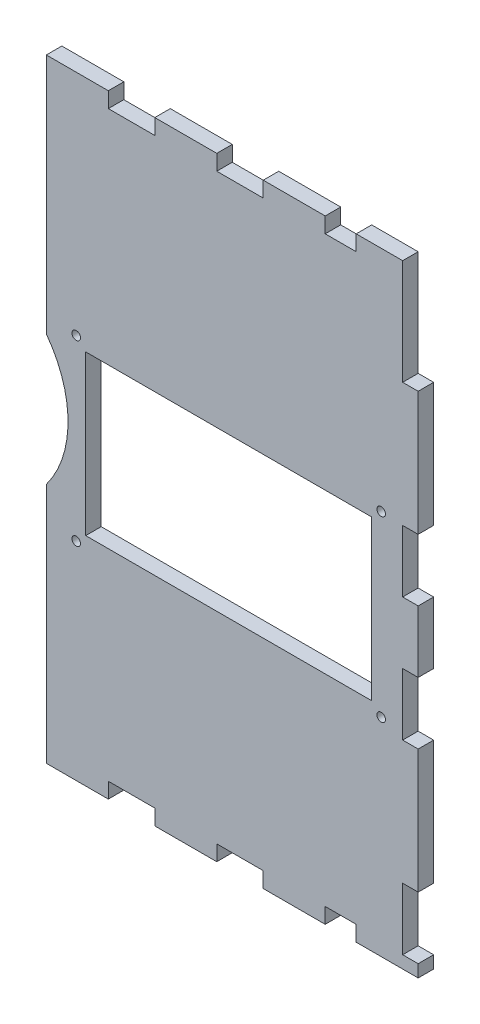
SolidWorks part; units mm, degrees
ref_plane "Front Plane" through (0, 0, 0) normal (0, 0, 1) x (1, 0, 0)
ref_plane "Top Plane" through (0, 0, 0) normal (0, 1, 0) x (1, 0, 0)
ref_plane "Right Plane" through (0, 0, 0) normal (1, 0, 0) x (0, 0, -1)
sketch "Sketch1" plane through (0, 0, 0) normal (0, 0, 1) x (1, 0, 0)
  line L1 (-133.35, 5.08) -> (-285.75, 5.08)
  line L2 (-133.35, 5.08) -> (-133.35, -246.38)
  line L3 (-133.35, -246.38) -> (-285.75, -246.38)
  line L4 (-285.75, 5.08) -> (-285.75, -246.38)
extrude "Boss-Extrude1" add sketch "Sketch1" along normal blind 6.35
sketch "Sketch2" plane through (0, 5.08, 0) normal (0, 1, 0) x (1, 0, 0)
  line L0 (-133.35, -6.35) -> (-285.75, -6.35) construction
  line L1 (-260.35, -6.35) -> (-241.3, -6.35)
  line L2 (-260.35, -6.35) -> (-260.35, 0)
  line L3 (-260.35, 0) -> (-241.3, 0)
  line L4 (-241.3, -6.35) -> (-241.3, 0)
  line L5 (-133.35, 0) -> (-285.75, 0) construction
  line L6 (-285.75, -6.35) -> (-285.75, 0) construction
  line L7 (-215.9, -6.35) -> (-196.85, -6.35)
  line L8 (-215.9, -6.35) -> (-215.9, 0)
  line L9 (-215.9, 0) -> (-196.85, 0)
  line L10 (-196.85, -6.35) -> (-196.85, 0)
  line L11 (-171.45, -6.35) -> (-158.75, -6.35)
  line L12 (-171.45, -6.35) -> (-171.45, 0)
  line L13 (-171.45, 0) -> (-158.75, 0)
  line L14 (-158.75, -6.35) -> (-158.75, 0)
  line M9 (-133.35, 0) -> (-285.75, 0)
  line M11 (-285.75, -6.35) -> (-133.35, -6.35)
  dimension "D1" = 25.4
  dimension "D2" = 19.05
  dimension "D3" = 25.4
  dimension "D4" = 19.05
  dimension "D5" = 25.4
  dimension "D6" = 12.7
extrude "Cut-Extrude1" cut sketch "Sketch2" against normal blind 6.35 contours L4 L2 M11 M9 | L10 L8 M11 M9 | L14 L12 M11 M9
sketch "Sketch3" plane through (0, -246.38, 0) normal (0, -1, 0) x (1, 0, 0)
  line L0 (-285.75, 0) -> (-133.35, 0) construction
  line L1 (-260.35, 0) -> (-241.3, 0)
  line L2 (-260.35, 0) -> (-260.35, 6.35)
  line L3 (-260.35, 6.35) -> (-241.3, 6.35)
  line L4 (-241.3, 0) -> (-241.3, 6.35)
  line L5 (-285.75, 6.35) -> (-133.35, 6.35) construction
  line L6 (-285.75, 6.35) -> (-285.75, 0) construction
  line L7 (-215.9, 0) -> (-196.85, 0)
  line L8 (-215.9, 0) -> (-215.9, 6.35)
  line L9 (-215.9, 6.35) -> (-196.85, 6.35)
  line L10 (-196.85, 0) -> (-196.85, 6.35)
  line L11 (-171.45, 0) -> (-158.75, 0)
  line L12 (-171.45, 0) -> (-171.45, 6.35)
  line L13 (-171.45, 6.35) -> (-158.75, 6.35)
  line L14 (-158.75, 0) -> (-158.75, 6.35)
  line L16 (-196.85, 6.35) -> (-196.85, 0) construction
  dimension "D1" = 25.4
  dimension "D2" = 19.05
  dimension "D3" = 25.4
  dimension "D4" = 19.05
  dimension "D5" = 25.4
  dimension "D6" = 12.7
extrude "Cut-Extrude2" cut sketch "Sketch3" against normal blind 6.35 and the other way through all
sketch "Sketch4" plane through (0, 0, 6.35) normal (0, 0, 1) x (1, 0, 0)
  line L0 (-133.35, -246.38) -> (-133.35, 5.08) construction
  line L3 (-133.35, -215.9) -> (-139.7, -215.9)
  line L5 (-133.35, -165.1) -> (-139.7, -165.1)
  line L6 (-133.35, -165.1) -> (-133.35, -139.7)
  line L7 (-133.35, -139.7) -> (-139.7, -139.7)
  line L8 (-139.7, -165.1) -> (-139.7, -139.7)
  line L9 (-133.35, 5.08) -> (-158.75, 5.08) construction
  line L10 (-133.35, -114.3) -> (-139.7, -114.3)
  line L11 (-133.35, -114.3) -> (-133.35, -88.9)
  line L12 (-133.35, -88.9) -> (-139.7, -88.9)
  line L13 (-139.7, -114.3) -> (-139.7, -88.9)
  line L14 (-133.35, -38.1) -> (-139.7, -38.1)
  line L15 (-133.35, -38.1) -> (-133.35, 5.08)
  line L16 (-133.35, 5.08) -> (-139.7, 5.08)
  line L17 (-139.7, -38.1) -> (-139.7, 5.08)
  line L18 (-139.7, -215.9) -> (-139.7, -241.3)
  line L19 (-139.7, -241.3) -> (-133.35, -241.3)
  line L20 (-133.35, -241.3) -> (-133.35, -215.9)
  line L21 (-158.75, -246.38) -> (-133.35, -246.38) construction
  line M24 (-133.35, -246.38) -> (-133.35, 5.08)
  line M25 (-133.35, 5.08) -> (-158.75, 5.08)
  dimension "D2" = 6.35
  dimension "D3" = 6.35
  dimension "D4" = 6.35
  dimension "D5" = 25.4
  dimension "D6" = 50.8
  dimension "D7" = 25.4
  dimension "D8" = 25.4
  dimension "D9" = 25.4
  dimension "D10" = 50.8
  dimension "D11" = 43.18
  dimension "D12" = 5.08
extrude "Cut-Extrude3" cut sketch "Sketch4" against normal blind 6.35 contours L8 L5 L7 M24 | L13 L10 L12 M24 | L17 L14 M24 M25 | L18 L19 L3 M24
sketch "Sketch5" plane through (0, 0, 6.35) normal (0, 0, 1) x (1, 0, 0)
  line L0 (-285.75, 5.08) -> (-285.75, -246.38) construction
  circle A0 centre (-321.31, -120.65) radius 44.45
  dimension "D1" = 88.9
  dimension "D2" = 35.56
extrude "Cut-Extrude4" cut sketch "Sketch5" against normal through all
sketch "Sketch6" plane through (0, 0, 6.35) normal (0, 0, 1) x (1, 0, 0)
  line L0 (-133.35, -139.7) -> (-133.35, -114.3) construction
  line L1 (-278.51, -166.37) -> (-143.51, -166.37) construction
  line L2 (-278.51, -166.37) -> (-278.51, -83.37) construction
  line L3 (-278.51, -83.37) -> (-143.51, -83.37) construction
  line L4 (-143.51, -166.37) -> (-143.51, -83.37) construction
  line L5 (-278.51, -166.37) -> (-143.51, -83.37) construction
  line L6 (-278.51, -83.37) -> (-143.51, -166.37) construction
  line L7 (-241.3, -246.38) -> (-215.9, -246.38) construction
  line L8 (-269.62, -157.48) -> (-269.62, -92.26)
  line L9 (-269.62, -92.26) -> (-152.4, -92.26)
  line L10 (-152.4, -157.48) -> (-152.4, -92.26)
  line L11 (-269.62, -157.48) -> (-152.4, -157.48)
  circle A0 centre (-273.51, -161.37) radius 1.75
  circle A1 centre (-273.51, -88.37) radius 1.75
  circle A2 centre (-148.51, -88.37) radius 1.75
  circle A3 centre (-148.51, -161.37) radius 1.75
  point P0 (-211.01, -124.87)
  dimension "D6" = 3.5
  dimension "D7" = 3.5
  dimension "D8" = 3.5
  dimension "D9" = 3.5
  dimension "D10" = 5
  dimension "D11" = 5
  dimension "D12" = 5
  dimension "D13" = 5
  dimension "D14" = 5
  dimension "D15" = 5
  dimension "D16" = 5
  dimension "D17" = 5
  dimension "D1" = 135
  dimension "D2" = 83
  dimension "D3" = 10.16
  dimension "D4" = 80.01
  dimension "D5" = 8.89
extrude "Cut-Extrude5" cut sketch "Sketch6" against normal through all contours L8 L11 L10 L9 | A1 | A0 | A2 | A3
